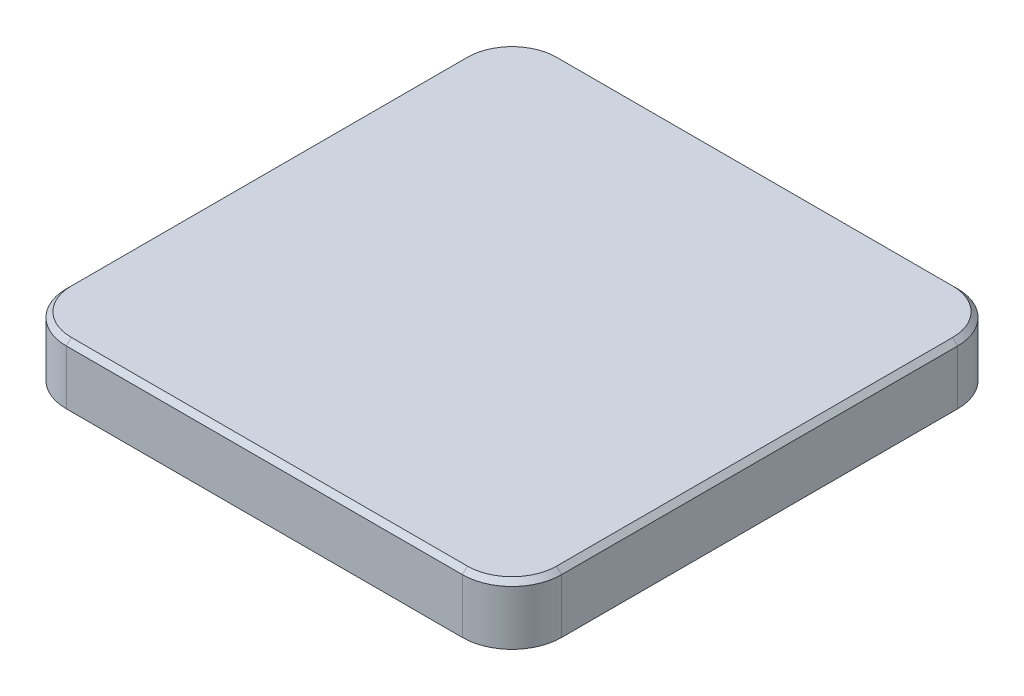
SolidWorks part; units mm, degrees
ref_plane "Front Plane" through (0, 0, 0) normal (0, 0, 1) x (1, 0, 0)
ref_plane "Top Plane" through (0, 0, 0) normal (0, 1, 0) x (1, 0, 0)
ref_plane "Right Plane" through (0, 0, 0) normal (1, 0, 0) x (0, 0, -1)
sketch "Sketch1" plane through (0, 0, 0) normal (0, 1, 0) x (1, 0, 0)
  line L1 (-40, -50) -> (40, -50)
  line L2 (-50, -40) -> (-50, 40)
  line L3 (-40, 50) -> (40, 50)
  line L4 (50, -40) -> (50, 40)
  arc A0 (-40, -50) -> (-50, -40) centre (-40, -40) cw
  arc A1 (40, -50) -> (50, -40) centre (40, -40) ccw
  arc A2 (50, 40) -> (40, 50) centre (40, 40) ccw
  arc A3 (-40, 50) -> (-50, 40) centre (-40, 40) ccw
  point P0 (0, 0)
  dimension "D1" = 10
extrude "Boss-Extrude1" add sketch "Sketch1" along normal mid plane 12
chamfer "Chamfer1" distance 1 angle 45 8 edges at (50, 6, 0) (0, 6, -50) (-47.0711, 6, -47.0711) (47.0711, 6, -47.0711) (-50, 6, 0) (-47.0711, 6, 47.0711) (47.0711, 6, 47.0711) (0, 6, 50)
